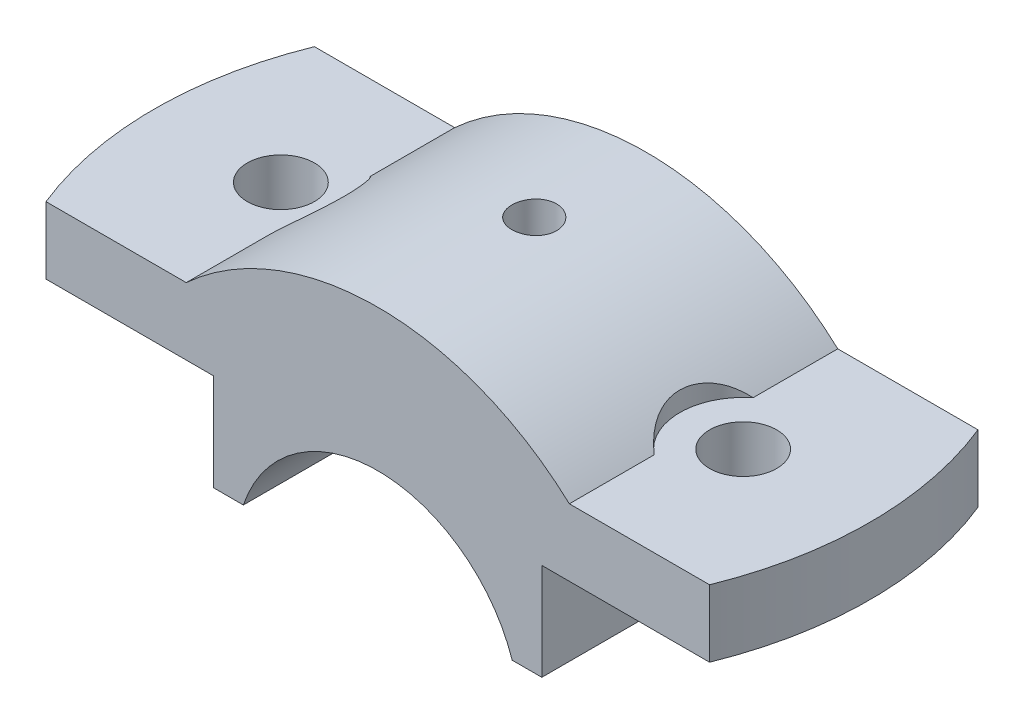
SolidWorks part; units mm, degrees
material "Malleable Cast Iron"
ref_plane "Front" through (0, 0, 0) normal (0, 0, 1) x (1, 0, 0)
ref_plane "Top" through (0, 0, 0) normal (0, 1, 0) x (1, 0, 0)
ref_plane "Right" through (0, 0, 0) normal (1, 0, 0) x (0, 0, -1)
sketch "Sketch1" plane through (0, 0, 0) normal (0, 0, 1) x (1, 0, 0)
  line L0 (0, 0) -> (0, 46.6461) construction
  line L1 (18.0278, 6) -> (22, 6)
  line L2 (22, 6) -> (22, 19)
  line L3 (22, 19) -> (50, 19)
  line L4 (50, 19) -> (50, 28)
  line L5 (50, 28) -> (25.6905, 28)
  line L6 (-18.0278, 6) -> (-22, 6)
  line L7 (-22, 6) -> (-22, 19)
  line L8 (-22, 19) -> (-50, 19)
  line L9 (-50, 19) -> (-50, 28)
  line L10 (-50, 28) -> (-25.6905, 28)
  arc A0 (25.6905, 28) -> (-25.6905, 28) centre (0, 0) ccw
  arc A1 (18.0278, 6) -> (-18.0278, 6) centre (0, 0) ccw
  dimension "D1" = 19
  dimension "D2" = 38
  dimension "D3" = 6
  dimension "D4" = 13
  dimension "D5" = 44
  dimension "D6" = 9
  dimension "D7" = 50
extrude "Boss-Extrude1" add sketch "Sketch1" along normal mid plane 36
sketch "Sketch3" plane through (0, 28, 0) normal (0, 1, 0) x (1, 0, 0)
  line L0 (-25.6905, 18) -> (-50, 18) construction
  line L1 (-50, -18) -> (-50, 18) construction
  line L2 (-25.6905, -18) -> (-50, -18) construction
  line L3 (-44.4972, 18) -> (-50, 18)
  line L4 (-50, -18) -> (-50, 18)
  line L5 (-44.4972, -18) -> (-50, -18)
  arc A0 (-44.4972, 18) -> (-44.4972, -18) centre (0, 0) ccw
  dimension "D1" = 48
extrude "Cut-Extrude1" cut sketch "Sketch3" against normal through all
hole_wizard "Ø12.0mm Dowel Hole3" positions "Sketch15" profile "Sketch14" hole size "Ø12.0" standard "ANSI Metric" end condition through all
sketch "Sketch15" plane through (0, 28, 0) normal (0, 1, 0) x (1, 0, 0)
  point P0 (-31, 0)
  dimension "D1" = 31
sketch "Sketch14" plane through (-31, 28, 0) normal (1, 0, 0) x (0, 0, 1)
  line L0 (0, 0) -> (0, 22)
  line L1 (0, 22) -> (4.5, 22)
  line L2 (4.5, 22) -> (4.5, 0)
  line L5 (4.5, 0) -> (0, 0)
  line L11 (0, -6.35) -> (0, 107.95) construction
  dimension "Thru Hole Dia." = 9
  dimension "Thru Hole Depth" = 22
sketch "Sketch17" plane through (0, 28, 0) normal (0, 1, 0) x (1, 0, 0)
  line L0 (-25.6905, -18) -> (-25.6905, 18) construction
  line L1 (-25.6905, -6.6377) -> (-25.6905, 6.6377)
  arc A0 (-25.6905, -6.6377) -> (-25.6905, 6.6377) centre (-31, 0) ccw
  dimension "D1" = 8.5
extrude "Cut-Extrude5" cut sketch "Sketch17" along normal blind 36
hole_wizard "CBORE for M6 Hex Head Bolt1" positions "3DSketch2" profile "Sketch20" counterbore size "M6" standard "ANSI Metric" end condition through all
sketch3d "3DSketch2"
  point P0 (0, 38, -2.9839)
  dimension "D1" = 0
sketch "Sketch20" plane through (0, 38, -2.9839) normal (1, 0, 0) x (0, 0, 1)
  line L0 (0, 0) -> (0, 32)
  line L1 (0, 32) -> (2.5, 32)
  line L2 (2.5, 13.495) -> (2.5, 32)
  line L3 (2.5, 13.495) -> (2.995, 13)
  line L4 (2.995, 13) -> (3, 13)
  line L5 (3, 13) -> (3, 0)
  line L7 (0, 0) -> (3, 0)
  line L9 (-2.5, 13.495) -> (-2.995, 13) construction
  line L11 (0, -6.35) -> (0, 107.95) construction
  dimension "Thru Hole Dia." = 5
  dimension "Thru Hole Depth" = 32
  dimension "C'Bore Dia." = 6
  dimension "C'Bore Depth" = 13
  dimension "Mid C'Sink Dia." = 5.99
  dimension "Mid C'Sink Angle" = 90
mirror "Mirror1" about plane through (0, 0, 0) normal (1, 0, 0) of "Cut-Extrude5", "Cut-Extrude1", "Ø12.0mm Dowel Hole3", "CBORE for M6 Hex Head Bolt1"
